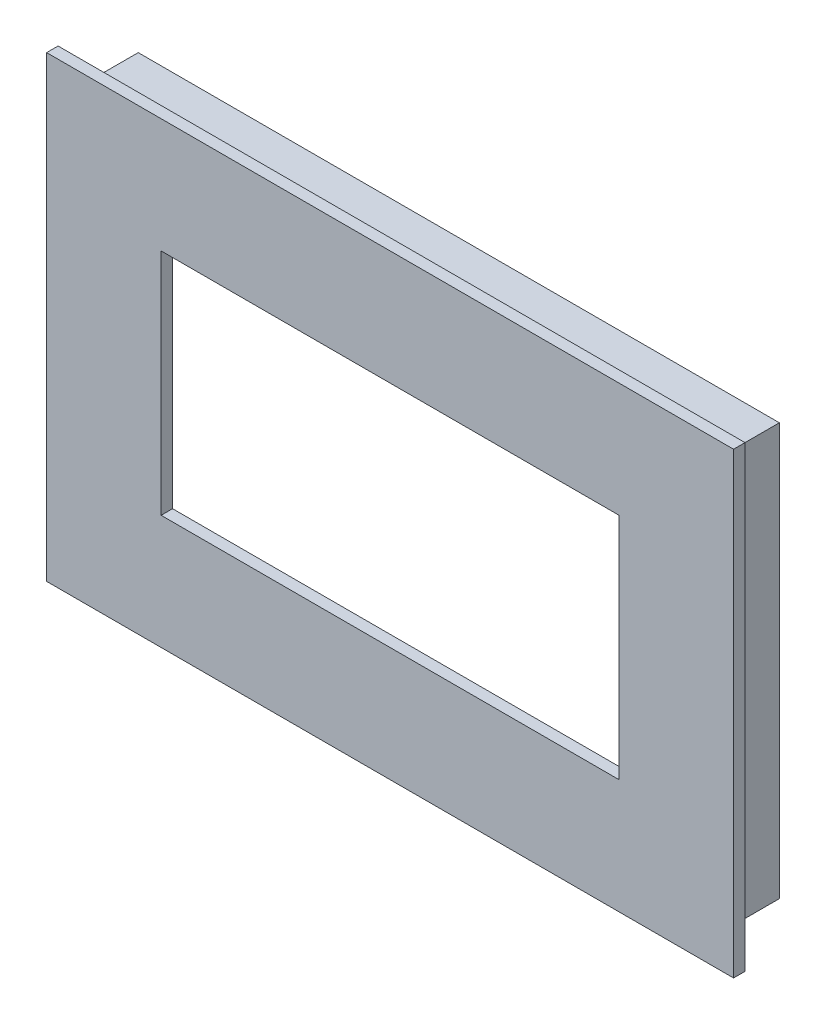
SolidWorks part; units mm, degrees
ref_plane "Front Plane" through (0, 0, 0) normal (0, 0, 1) x (1, 0, 0)
ref_plane "Top Plane" through (0, 0, 0) normal (0, 1, 0) x (1, 0, 0)
ref_plane "Right Plane" through (0, 0, 0) normal (1, 0, 0) x (0, 0, -1)
sketch "Sketch1" plane through (0, 0, 0) normal (0, 0, 1) x (1, 0, 0)
  line L1 (28, 18) -> (-28, 18)
  line L2 (28, 18) -> (28, -18)
  line L3 (28, -18) -> (-28, -18)
  line L4 (-28, 18) -> (-28, -18)
  line L5 (28, 18) -> (-28, -18) construction
  line L6 (28, -18) -> (-28, 18) construction
  line L10 (27, 17) -> (-27, 17)
  line L11 (-27, 17) -> (-27, -17)
  line L12 (27, -17) -> (-27, -17)
  line L13 (27, 17) -> (27, -17)
  point P0 (0, 0)
  dimension "D1" = 36
  dimension "D2" = 56
  dimension "D3" = 1
extrude "Boss-Extrude1" add sketch "Sketch1" along normal blind 5
sketch "Sketch3" plane through (0, 0, 5) normal (0, 0, 1) x (1, 0, 0)
  line L14 (30, -20) -> (30, 20)
  line L15 (-30, -20) -> (30, -20)
  line L16 (-30, 20) -> (-30, -20)
  line L17 (30, 20) -> (-30, 20)
  line L18 (30, -20) -> (30, 20)
  line L19 (-30, -20) -> (30, -20)
  line L20 (-30, 20) -> (-30, -20)
  line L21 (30, 20) -> (-30, 20)
  dimension "D1" = 2
extrude "Boss-Extrude3" add sketch "Sketch3" along normal blind 1
sketch "Sketch4" plane through (0, 0, 6) normal (0, 0, 1) x (1, 0, 0)
  line L12 (-20, -10) -> (20, -10)
  line L13 (20, -10) -> (20, 10)
  line L14 (20, 10) -> (-20, 10)
  line L15 (-20, 10) -> (-20, -10)
  line L16 (-20, -10) -> (20, -10)
  line L17 (20, -10) -> (20, 10)
  line L18 (20, 10) -> (-20, 10)
  line L19 (-20, 10) -> (-20, -10)
  dimension "D1" = 10
extrude "Cut-Extrude2" cut sketch "Sketch4" against normal through all
